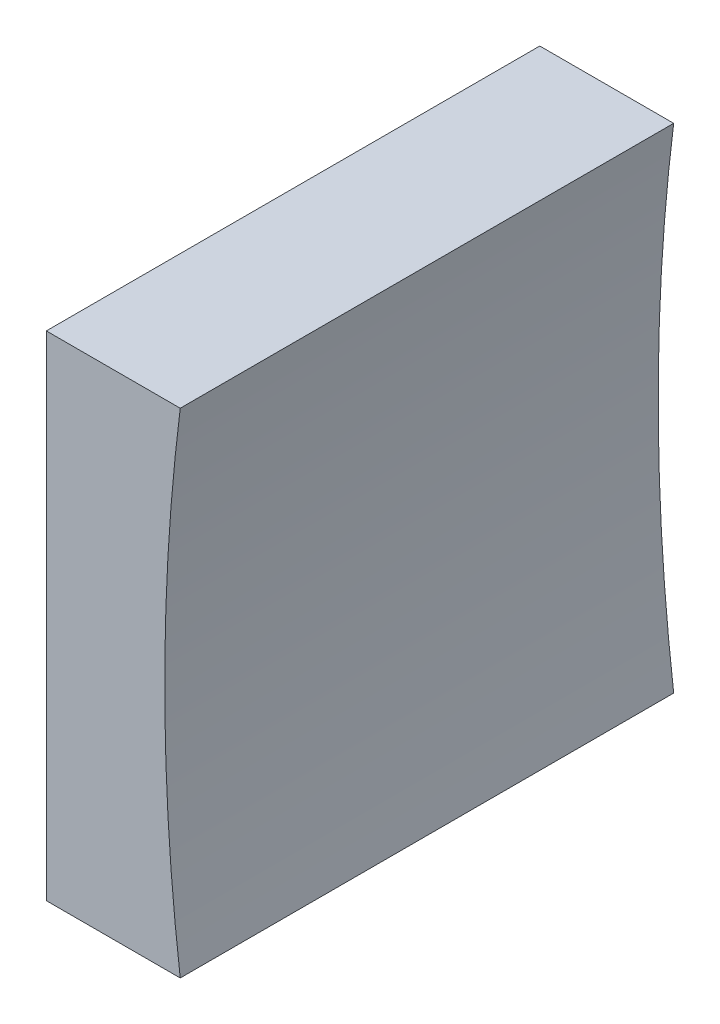
SolidWorks part; units mm, degrees
ref_plane "前视基准面" through (0, 0, 0) normal (0, 0, 1) x (1, 0, 0)
ref_plane "上视基准面" through (0, 0, 0) normal (0, 1, 0) x (1, 0, 0)
ref_plane "右视基准面" through (0, 0, 0) normal (1, 0, 0) x (0, 0, -1)
sketch "草图1" plane through (0, 0, 0) normal (0, 0, 1) x (1, 0, 0)
  line L0 (278.655, 66.8579) -> (298.183, 66.8579) construction
  line L1 (284.7071, 66.8579) -> (284.7071, 79.3579)
  line L2 (284.7071, 79.3579) -> (291.4915, 79.3579)
  line L3 (291.4915, 54.3579) -> (284.7071, 54.3579)
  line L4 (284.7071, 54.3579) -> (284.7071, 66.8579)
  arc A0 (291.4915, 79.3579) -> (291.4915, 54.3579) centre (390.7071, 66.8579) ccw
  dimension "D1" = 100
extrude "凸台-拉伸1" add sketch "草图1" along normal blind 25
